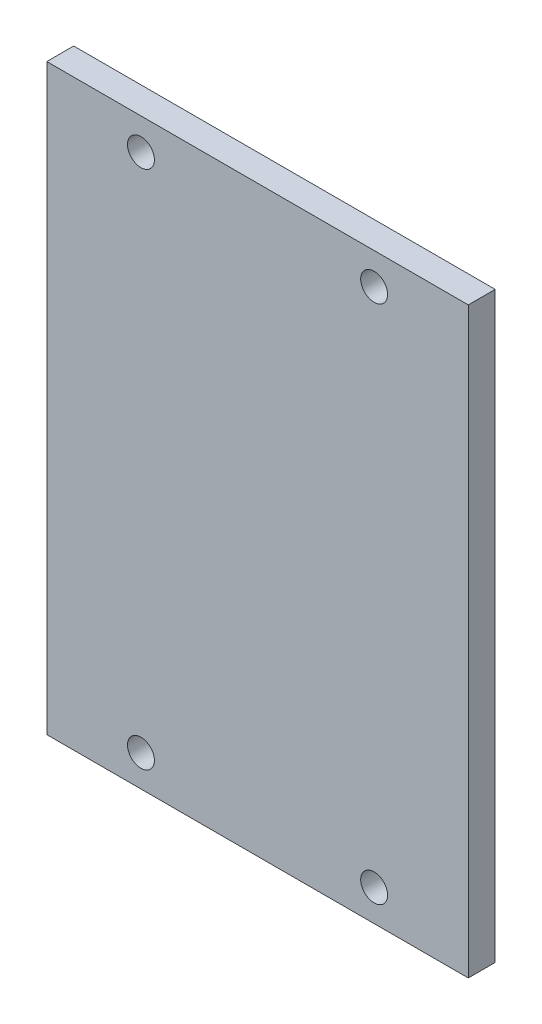
SolidWorks part; units mm, degrees
ref_plane "Front Plane" through (0, 0, 0) normal (0, 0, 1) x (1, 0, 0)
ref_plane "Top Plane" through (0, 0, 0) normal (0, 1, 0) x (1, 0, 0)
ref_plane "Right Plane" through (0, 0, 0) normal (1, 0, 0) x (0, 0, -1)
sketch "Sketch1" plane through (0, 0, 0) normal (0, 0, 1) x (1, 0, 0)
  line L1 (-23.5, -32.5) -> (23.5, -32.5)
  line L2 (-23.5, -32.5) -> (-23.5, 32.5)
  line L3 (-23.5, 32.5) -> (23.5, 32.5)
  line L4 (23.5, -32.5) -> (23.5, 32.5)
  line L5 (-23.5, -32.5) -> (23.5, 32.5) construction
  line L6 (-23.5, 32.5) -> (23.5, -32.5) construction
  point P0 (0, 0)
  dimension "D1" = 47
  dimension "D2" = 65
extrude "Boss-Extrude1" add sketch "Sketch1" along normal blind 3
hole_wizard "Ø3.0mm Dowel Hole1" positions "Sketch2" profile "Sketch3" hole size "Ø3.0" standard "ANSI Metric"
sketch "Sketch2" plane through (0, 0, 3) normal (0, 0, 1) x (1, 0, 0)
  line L0 (-23.5, 32.5) -> (-23.5, -32.5) construction
  line L2 (-23.5, -32.5) -> (23.5, -32.5) construction
  line L3 (0, -1.65) -> (0, 1.65) construction
  line L4 (1.65, 0) -> (-1.65, 0) construction
  point P0 (-13, -29)
  point P17 (13, -29)
  point P20 (13, 29)
  point P21 (-13, 29)
  dimension "D1" = 10.5
  dimension "D2" = 3.5
sketch "Sketch3" plane through (-13, -29, 3) normal (1, 0, 0) x (0, -1, 0)
  line L0 (0, 0) -> (0, 4.9013)
  line L1 (0, 4.9013) -> (1.5, 4)
  line L2 (1.5, 4) -> (1.5, 0)
  line L5 (1.5, 0) -> (0, 0)
  line L10 (0, 4.9013) -> (-1.5, 4) construction
  line L11 (0, -6.35) -> (0, 107.95) construction
  dimension "Hole Dia." = 3
  dimension "Hole Depth" = 4
  dimension "Drill Angle" = 118
